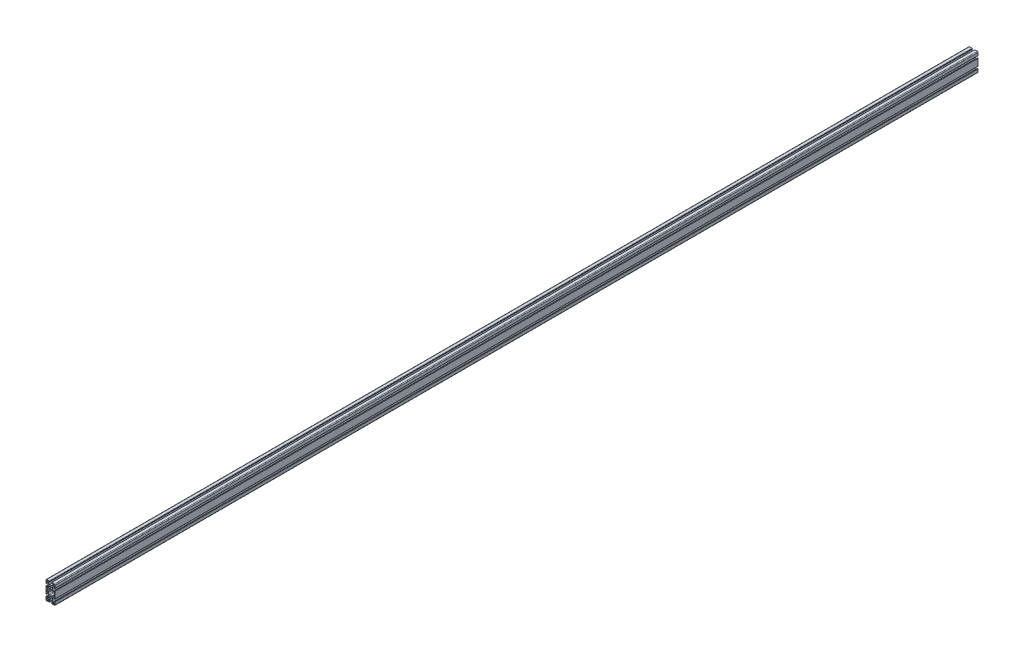
SolidWorks part; units mm, degrees
ref_plane "Front Plane" through (0, 0, 0) normal (0, 0, 1) x (1, 0, 0)
ref_plane "Top Plane" through (0, 0, 0) normal (0, 1, 0) x (1, 0, 0)
ref_plane "Right Plane" through (0, 0, 0) normal (1, 0, 0) x (0, 0, -1)
ref_plane "Plane1" through (0, 0, -4000) normal (0, 0, -1) x (-1, 0, 0)
sketch "Sketch1" plane through (0, 0, -4000) normal (0, 0, -1) x (-1, 0, 0)
  line L0 (18.3499, 55.5501) -> (18.3499, 52.5701)
  line L1 (17.7199, 51.9401) -> (13.2099, 51.9401)
  line L2 (11.9399, 53.2101) -> (11.9399, 57.7201)
  line L3 (12.5699, 58.3501) -> (15.5499, 58.3501)
  line L4 (18.3499, -12.5701) -> (18.3499, -15.5501)
  line L5 (15.5499, -18.3501) -> (12.5699, -18.3501)
  line L6 (11.9399, -17.7201) -> (11.9399, -13.2101)
  line L7 (13.2099, -11.9401) -> (17.7199, -11.9401)
  line L8 (16.7, 25.1794) -> (16.7, 14.8206)
  line L9 (15.43, 13.5506) -> (11.7432, 13.5506)
  line L10 (10.8451, 13.1786) -> (6.5812, 8.9146)
  line L11 (3.2224, 7.5234) -> (-3.2224, 7.5234)
  line L12 (-6.5812, 8.9146) -> (-10.8451, 13.1786)
  line L13 (-11.7432, 13.5506) -> (-15.43, 13.5506)
  line L14 (-16.7, 14.8206) -> (-16.7, 25.1794)
  line L15 (-15.43, 26.4494) -> (-11.7432, 26.4494)
  line L16 (-10.8451, 26.8214) -> (-6.5812, 31.0854)
  line L17 (-3.2224, 32.4766) -> (3.2224, 32.4766)
  line L18 (6.5812, 31.0854) -> (10.8451, 26.8214)
  line L19 (11.7432, 26.4494) -> (15.43, 26.4494)
  line L20 (-11.9399, 57.7201) -> (-11.9399, 53.2101)
  line L21 (-13.2099, 51.9401) -> (-17.7199, 51.9401)
  line L22 (-18.3499, 52.5701) -> (-18.3499, 55.5501)
  line L23 (-15.5499, 58.3501) -> (-12.5699, 58.3501)
  line L24 (-11.9399, -13.2101) -> (-11.9399, -17.7201)
  line L25 (-12.5699, -18.3501) -> (-15.5499, -18.3501)
  line L26 (-18.3499, -15.5501) -> (-18.3499, -12.5701)
  line L27 (-17.7199, -11.9401) -> (-13.2099, -11.9401)
  line L28 (18.5197, 35.94) -> (17.8048, 35.94)
  line L29 (15.94, 34.0752) -> (15.94, 32.7193)
  line L30 (15.94, 32.7193) -> (16.7, 32.7193)
  line L31 (16.7, 32.7193) -> (16.7, 31.0517)
  line L32 (15.3633, 29.715) -> (12.9871, 29.715)
  line L33 (12.3578, 29.9757) -> (9.0912, 33.2422)
  line L34 (7.7, 36.601) -> (7.7, 43.399)
  line L35 (9.0912, 46.7578) -> (12.3578, 50.0243)
  line L36 (12.9871, 50.285) -> (15.3633, 50.285)
  line L37 (16.7, 48.9483) -> (16.7, 47.2807)
  line L38 (16.7, 47.2807) -> (15.94, 47.2807)
  line L39 (15.94, 47.2807) -> (15.94, 45.9248)
  line L40 (17.8048, 44.06) -> (18.5197, 44.06)
  line L41 (20, 45.5403) -> (20, 56.83)
  line L42 (16.83, 60) -> (5.6299, 60)
  line L43 (4.0599, 58.43) -> (4.0599, 57.51)
  line L44 (5.6299, 55.94) -> (6.6963, 55.94)
  line L45 (6.6963, 55.94) -> (6.6963, 56.715)
  line L46 (6.6963, 56.715) -> (9.0199, 56.715)
  line L47 (10.2899, 55.445) -> (10.2899, 52.992)
  line L48 (10.0292, 52.3627) -> (6.5812, 48.9146)
  line L49 (3.2224, 47.5234) -> (-3.2224, 47.5234)
  line L50 (-6.5812, 48.9146) -> (-10.0292, 52.3627)
  line L51 (-10.2899, 52.992) -> (-10.2899, 55.445)
  line L52 (-9.0199, 56.715) -> (-6.6963, 56.715)
  line L53 (-6.6963, 56.715) -> (-6.6963, 55.94)
  line L54 (-6.6963, 55.94) -> (-5.6299, 55.94)
  line L55 (-4.0599, 57.51) -> (-4.0599, 58.43)
  line L56 (-5.6299, 60) -> (-16.83, 60)
  line L57 (-20, 56.83) -> (-20, 45.5403)
  line L58 (-18.5197, 44.06) -> (-17.8048, 44.06)
  line L59 (-15.94, 45.9248) -> (-15.94, 47.2807)
  line L60 (-15.94, 47.2807) -> (-16.7, 47.2807)
  line L61 (-16.7, 47.2807) -> (-16.7, 48.9483)
  line L62 (-15.3633, 50.285) -> (-12.9871, 50.285)
  line L63 (-12.3578, 50.0243) -> (-9.0912, 46.7578)
  line L64 (-7.7, 43.399) -> (-7.7, 36.601)
  line L65 (-9.0912, 33.2422) -> (-12.3578, 29.9757)
  line L66 (-12.9871, 29.715) -> (-15.3633, 29.715)
  line L67 (-16.7, 31.0517) -> (-16.7, 32.7193)
  line L68 (-16.7, 32.7193) -> (-15.94, 32.7193)
  line L69 (-15.94, 32.7193) -> (-15.94, 34.0752)
  line L70 (-17.8048, 35.94) -> (-18.5197, 35.94)
  line L71 (-20, 34.4597) -> (-20, 5.5403)
  line L72 (-18.5197, 4.06) -> (-17.8048, 4.06)
  line L73 (-15.94, 5.9248) -> (-15.94, 7.2807)
  line L74 (-15.94, 7.2807) -> (-16.7, 7.2807)
  line L75 (-16.7, 7.2807) -> (-16.7, 9.015)
  line L76 (-15.43, 10.285) -> (-12.9871, 10.285)
  line L77 (-12.3578, 10.0243) -> (-9.0912, 6.7578)
  line L78 (-7.7, 3.399) -> (-7.7, -3.399)
  line L79 (-9.0912, -6.7578) -> (-12.3578, -10.0243)
  line L80 (-12.9871, -10.285) -> (-15.3633, -10.285)
  line L81 (-16.7, -8.9483) -> (-16.7, -7.2807)
  line L82 (-16.7, -7.2807) -> (-15.94, -7.2807)
  line L83 (-15.94, -7.2807) -> (-15.94, -5.9248)
  line L84 (-17.8048, -4.06) -> (-18.5197, -4.06)
  line L85 (-20, -5.5403) -> (-20, -16.83)
  line L86 (-16.83, -20) -> (-5.6299, -20)
  line L87 (-4.0599, -18.43) -> (-4.0599, -17.51)
  line L88 (-5.6299, -15.94) -> (-6.6963, -15.94)
  line L89 (-6.6963, -15.94) -> (-6.6963, -16.715)
  line L90 (-6.6963, -16.715) -> (-9.0199, -16.715)
  line L91 (-10.2899, -15.445) -> (-10.2899, -12.992)
  line L92 (-10.0292, -12.3627) -> (-6.5812, -8.9146)
  line L93 (-3.2224, -7.5234) -> (3.2224, -7.5234)
  line L94 (6.5812, -8.9146) -> (10.0292, -12.3627)
  line L95 (10.2899, -12.992) -> (10.2899, -15.3025)
  line L96 (9.0199, -16.5725) -> (6.8403, -16.5725)
  line L97 (6.8403, -16.5725) -> (6.8403, -15.94)
  line L98 (6.8403, -15.94) -> (5.6299, -15.94)
  line L99 (4.0599, -17.51) -> (4.0599, -18.43)
  line L100 (5.6299, -20) -> (16.83, -20)
  line L101 (20, -16.83) -> (20, -5.5403)
  line L102 (18.5197, -4.06) -> (17.8048, -4.06)
  line L103 (15.94, -5.9248) -> (15.94, -7.2807)
  line L104 (15.94, -7.2807) -> (16.7, -7.2807)
  line L105 (16.7, -7.2807) -> (16.7, -8.9483)
  line L106 (15.3633, -10.285) -> (12.9871, -10.285)
  line L107 (12.3578, -10.0243) -> (9.0912, -6.7578)
  line L108 (7.7, -3.399) -> (7.7, 3.399)
  line L109 (9.0912, 6.7578) -> (12.3578, 10.0243)
  line L110 (12.9871, 10.285) -> (15.43, 10.285)
  line L111 (16.7, 9.015) -> (16.7, 7.2807)
  line L112 (16.7, 7.2807) -> (15.94, 7.2807)
  line L113 (15.94, 7.2807) -> (15.94, 5.9248)
  line L114 (17.8048, 4.06) -> (18.5197, 4.06)
  line L115 (20, 5.5403) -> (20, 34.4597)
  arc A0 (15.5499, 58.3501) -> (18.3499, 55.5501) centre (15.5499, 55.5501) cw
  arc A1 (18.3499, 52.5701) -> (17.7199, 51.9401) centre (17.7199, 52.5701) cw
  arc A2 (13.2099, 51.9401) -> (11.9399, 53.2101) centre (13.2099, 53.2101) cw
  arc A3 (11.9399, 57.7201) -> (12.5699, 58.3501) centre (12.5699, 57.7201) cw
  arc A4 (18.3499, -15.5501) -> (15.5499, -18.3501) centre (15.5499, -15.5501) cw
  arc A5 (12.5699, -18.3501) -> (11.9399, -17.7201) centre (12.5699, -17.7201) cw
  arc A6 (11.9399, -13.2101) -> (13.2099, -11.9401) centre (13.2099, -13.2101) cw
  arc A7 (17.7199, -11.9401) -> (18.3499, -12.5701) centre (17.7199, -12.5701) cw
  arc A8 (16.7, 14.8206) -> (15.43, 13.5506) centre (15.43, 14.8206) cw
  arc A9 (11.7432, 13.5506) -> (10.8451, 13.1786) centre (11.7432, 12.2806) ccw
  arc A10 (6.5812, 8.9146) -> (3.2224, 7.5234) centre (3.2224, 12.2734) cw
  arc A11 (-3.2224, 7.5234) -> (-6.5812, 8.9146) centre (-3.2224, 12.2734) cw
  arc A12 (-10.8451, 13.1786) -> (-11.7432, 13.5506) centre (-11.7432, 12.2806) ccw
  arc A13 (-15.43, 13.5506) -> (-16.7, 14.8206) centre (-15.43, 14.8206) cw
  arc A14 (-16.7, 25.1794) -> (-15.43, 26.4494) centre (-15.43, 25.1794) cw
  arc A15 (-11.7432, 26.4494) -> (-10.8451, 26.8214) centre (-11.7432, 27.7194) ccw
  arc A16 (-6.5812, 31.0854) -> (-3.2224, 32.4766) centre (-3.2224, 27.7266) cw
  arc A17 (3.2224, 32.4766) -> (6.5812, 31.0854) centre (3.2224, 27.7266) cw
  arc A18 (10.8451, 26.8214) -> (11.7432, 26.4494) centre (11.7432, 27.7194) ccw
  arc A19 (15.43, 26.4494) -> (16.7, 25.1794) centre (15.43, 25.1794) cw
  circle A20 centre (0, 0) radius 3.4
  circle A21 centre (0, 40) radius 3.25
  arc A22 (-11.9399, 53.2101) -> (-13.2099, 51.9401) centre (-13.2099, 53.2101) cw
  arc A23 (-17.7199, 51.9401) -> (-18.3499, 52.5701) centre (-17.7199, 52.5701) cw
  arc A24 (-18.3499, 55.5501) -> (-15.5499, 58.3501) centre (-15.5499, 55.5501) cw
  arc A25 (-12.5699, 58.3501) -> (-11.9399, 57.7201) centre (-12.5699, 57.7201) cw
  arc A26 (-13.2099, -11.9401) -> (-11.9399, -13.2101) centre (-13.2099, -13.2101) cw
  arc A27 (-11.9399, -17.7201) -> (-12.5699, -18.3501) centre (-12.5699, -17.7201) cw
  arc A28 (-15.5499, -18.3501) -> (-18.3499, -15.5501) centre (-15.5499, -15.5501) cw
  arc A29 (-18.3499, -12.5701) -> (-17.7199, -11.9401) centre (-17.7199, -12.5701) cw
  arc A30 (20, 34.4597) -> (18.5197, 35.94) centre (18.5197, 34.4597) ccw
  arc A31 (17.8048, 35.94) -> (15.94, 34.0752) centre (17.8048, 34.0752) ccw
  arc A32 (16.7, 31.0517) -> (15.3633, 29.715) centre (15.3633, 31.0517) cw
  arc A33 (12.9871, 29.715) -> (12.3578, 29.9757) centre (12.9871, 30.605) cw
  arc A34 (9.0912, 33.2422) -> (7.7, 36.601) centre (12.45, 36.601) cw
  arc A35 (7.7, 43.399) -> (9.0912, 46.7578) centre (12.45, 43.399) cw
  arc A36 (12.3578, 50.0243) -> (12.9871, 50.285) centre (12.9871, 49.395) cw
  arc A37 (15.3633, 50.285) -> (16.7, 48.9483) centre (15.3633, 48.9483) cw
  arc A38 (15.94, 45.9248) -> (17.8048, 44.06) centre (17.8048, 45.9248) ccw
  arc A39 (18.5197, 44.06) -> (20, 45.5403) centre (18.5197, 45.5403) ccw
  arc A40 (20, 56.83) -> (16.83, 60) centre (16.83, 56.83) ccw
  arc A41 (5.6299, 60) -> (4.0599, 58.43) centre (5.6299, 58.43) ccw
  arc A42 (4.0599, 57.51) -> (5.6299, 55.94) centre (5.6299, 57.51) ccw
  arc A43 (9.0199, 56.715) -> (10.2899, 55.445) centre (9.0199, 55.445) cw
  arc A44 (10.2899, 52.992) -> (10.0292, 52.3627) centre (9.3999, 52.992) cw
  arc A45 (6.5812, 48.9146) -> (3.2224, 47.5234) centre (3.2224, 52.2734) cw
  arc A46 (-3.2224, 47.5234) -> (-6.5812, 48.9146) centre (-3.2224, 52.2734) cw
  arc A47 (-10.0292, 52.3627) -> (-10.2899, 52.992) centre (-9.3999, 52.992) cw
  arc A48 (-10.2899, 55.445) -> (-9.0199, 56.715) centre (-9.0199, 55.445) cw
  arc A49 (-5.6299, 55.94) -> (-4.0599, 57.51) centre (-5.6299, 57.51) ccw
  arc A50 (-4.0599, 58.43) -> (-5.6299, 60) centre (-5.6299, 58.43) ccw
  arc A51 (-16.83, 60) -> (-20, 56.83) centre (-16.83, 56.83) ccw
  arc A52 (-20, 45.5403) -> (-18.5197, 44.06) centre (-18.5197, 45.5403) ccw
  arc A53 (-17.8048, 44.06) -> (-15.94, 45.9248) centre (-17.8048, 45.9248) ccw
  arc A54 (-16.7, 48.9483) -> (-15.3633, 50.285) centre (-15.3633, 48.9483) cw
  arc A55 (-12.9871, 50.285) -> (-12.3578, 50.0243) centre (-12.9871, 49.395) cw
  arc A56 (-9.0912, 46.7578) -> (-7.7, 43.399) centre (-12.45, 43.399) cw
  arc A57 (-7.7, 36.601) -> (-9.0912, 33.2422) centre (-12.45, 36.601) cw
  arc A58 (-12.3578, 29.9757) -> (-12.9871, 29.715) centre (-12.9871, 30.605) cw
  arc A59 (-15.3633, 29.715) -> (-16.7, 31.0517) centre (-15.3633, 31.0517) cw
  arc A60 (-15.94, 34.0752) -> (-17.8048, 35.94) centre (-17.8048, 34.0752) ccw
  arc A61 (-18.5197, 35.94) -> (-20, 34.4597) centre (-18.5197, 34.4597) ccw
  arc A62 (-20, 5.5403) -> (-18.5197, 4.06) centre (-18.5197, 5.5403) ccw
  arc A63 (-17.8048, 4.06) -> (-15.94, 5.9248) centre (-17.8048, 5.9248) ccw
  arc A64 (-16.7, 9.015) -> (-15.43, 10.285) centre (-15.43, 9.015) cw
  arc A65 (-12.9871, 10.285) -> (-12.3578, 10.0243) centre (-12.9871, 9.395) cw
  arc A66 (-9.0912, 6.7578) -> (-7.7, 3.399) centre (-12.45, 3.399) cw
  arc A67 (-7.7, -3.399) -> (-9.0912, -6.7578) centre (-12.45, -3.399) cw
  arc A68 (-12.3578, -10.0243) -> (-12.9871, -10.285) centre (-12.9871, -9.395) cw
  arc A69 (-15.3633, -10.285) -> (-16.7, -8.9483) centre (-15.3633, -8.9483) cw
  arc A70 (-15.94, -5.9248) -> (-17.8048, -4.06) centre (-17.8048, -5.9248) ccw
  arc A71 (-18.5197, -4.06) -> (-20, -5.5403) centre (-18.5197, -5.5403) ccw
  arc A72 (-20, -16.83) -> (-16.83, -20) centre (-16.83, -16.83) ccw
  arc A73 (-5.6299, -20) -> (-4.0599, -18.43) centre (-5.6299, -18.43) ccw
  arc A74 (-4.0599, -17.51) -> (-5.6299, -15.94) centre (-5.6299, -17.51) ccw
  arc A75 (-9.0199, -16.715) -> (-10.2899, -15.445) centre (-9.0199, -15.445) cw
  arc A76 (-10.2899, -12.992) -> (-10.0292, -12.3627) centre (-9.3999, -12.992) cw
  arc A77 (-6.5812, -8.9146) -> (-3.2224, -7.5234) centre (-3.2224, -12.2734) cw
  arc A78 (3.2224, -7.5234) -> (6.5812, -8.9146) centre (3.2224, -12.2734) cw
  arc A79 (10.0292, -12.3627) -> (10.2899, -12.992) centre (9.3999, -12.992) cw
  arc A80 (10.2899, -15.3025) -> (9.0199, -16.5725) centre (9.0199, -15.3025) cw
  arc A81 (5.6299, -15.94) -> (4.0599, -17.51) centre (5.6299, -17.51) ccw
  arc A82 (4.0599, -18.43) -> (5.6299, -20) centre (5.6299, -18.43) ccw
  arc A83 (16.83, -20) -> (20, -16.83) centre (16.83, -16.83) ccw
  arc A84 (20, -5.5403) -> (18.5197, -4.06) centre (18.5197, -5.5403) ccw
  arc A85 (17.8048, -4.06) -> (15.94, -5.9248) centre (17.8048, -5.9248) ccw
  arc A86 (16.7, -8.9483) -> (15.3633, -10.285) centre (15.3633, -8.9483) cw
  arc A87 (12.9871, -10.285) -> (12.3578, -10.0243) centre (12.9871, -9.395) cw
  arc A88 (9.0912, -6.7578) -> (7.7, -3.399) centre (12.45, -3.399) cw
  arc A89 (7.7, 3.399) -> (9.0912, 6.7578) centre (12.45, 3.399) cw
  arc A90 (12.3578, 10.0243) -> (12.9871, 10.285) centre (12.9871, 9.395) cw
  arc A91 (15.43, 10.285) -> (16.7, 9.015) centre (15.43, 9.015) cw
  arc A92 (15.94, 5.9248) -> (17.8048, 4.06) centre (17.8048, 5.9248) ccw
  arc A93 (18.5197, 4.06) -> (20, 5.5403) centre (18.5197, 5.5403) ccw
extrude "Boss-Extrude1" add sketch "Sketch1" against normal blind 4000
